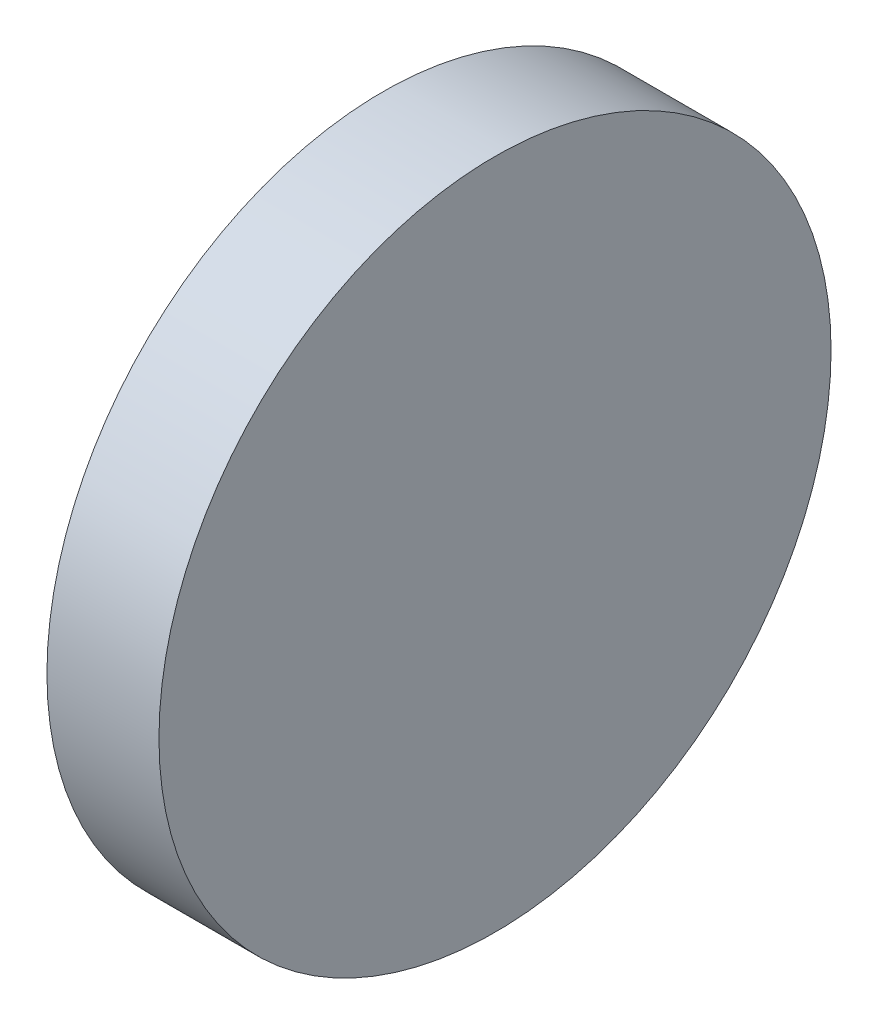
SolidWorks part; units mm, degrees
ref_plane "Front Plane" through (0, 0, 0) normal (0, 0, 1) x (1, 0, 0)
ref_plane "Top Plane" through (0, 0, 0) normal (0, 1, 0) x (1, 0, 0)
ref_plane "Right Plane" through (0, 0, 0) normal (1, 0, 0) x (0, 0, -1)
sketch "Sketch1" plane through (0, 0, 0) normal (1, 0, 0) x (0, 0, -1)
  circle A0 centre (0, 0) radius 3
  dimension "D1" = 6
extrude "Boss-Extrude1" add sketch "Sketch1" along normal blind 1
